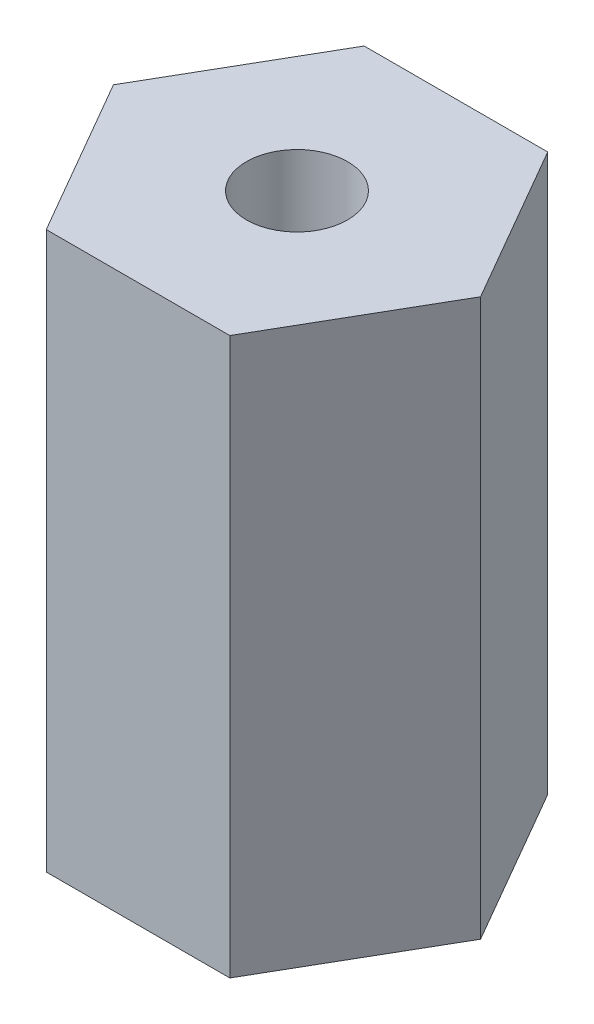
SolidWorks part; units mm, degrees
ref_plane "Front Plane" through (0, 0, 0) normal (0, 0, 1) x (1, 0, 0)
ref_plane "Top Plane" through (0, 0, 0) normal (0, 1, 0) x (1, 0, 0)
ref_plane "Right Plane" through (0, 0, 0) normal (1, 0, 0) x (0, 0, -1)
sketch "Sketch1" plane through (0, 0, 0) normal (0, 1, 0) x (1, 0, 0)
  line L9 (7.3323, 0) -> (3.6662, 6.35)
  line L10 (3.6662, 6.35) -> (-3.6662, 6.35)
  line L11 (-3.6662, 6.35) -> (-7.3323, 0)
  line L12 (-7.3323, 0) -> (-3.6662, -6.35)
  line L13 (-3.6662, -6.35) -> (3.6662, -6.35)
  line L14 (3.6662, -6.35) -> (7.3323, 0)
  circle A0 centre (0, 0) radius 6.35 construction
  dimension "D1" = 12.7
extrude "Boss-Extrude1" add sketch "Sketch1" along normal blind 22.225
hole_wizard "#10-32 Tapped Hole1" positions "Sketch2" profile "Sketch4" tap size "#10-32" standard "ANSI Inch"
sketch "Sketch2" plane through (0, 22.225, 0) normal (0, 1, 0) x (1, 0, 0)
  point P0 (0, 0)
sketch "Sketch4" plane through (0, 22.225, 0) normal (1, 0, 0) x (0, 0, 1)
  line L0 (0, 0) -> (0, 14.8277)
  line L1 (0, 14.8277) -> (2.0193, 13.6144)
  line L2 (2.0193, 13.6144) -> (2.0193, 0)
  line L5 (2.0193, 0) -> (0, 0)
  line L10 (0, 14.8277) -> (-2.0193, 13.6144) construction
  line L11 (0, -6.35) -> (0, 107.95) construction
  dimension "Tap Drill Dia." = 4.0386
  dimension "Tap Drill Depth" = 13.6144
  dimension "Drill Angle" = 118
cosmetic thread "Hole Thread1" parameters "D1"=9.652, "D2"=4.826
